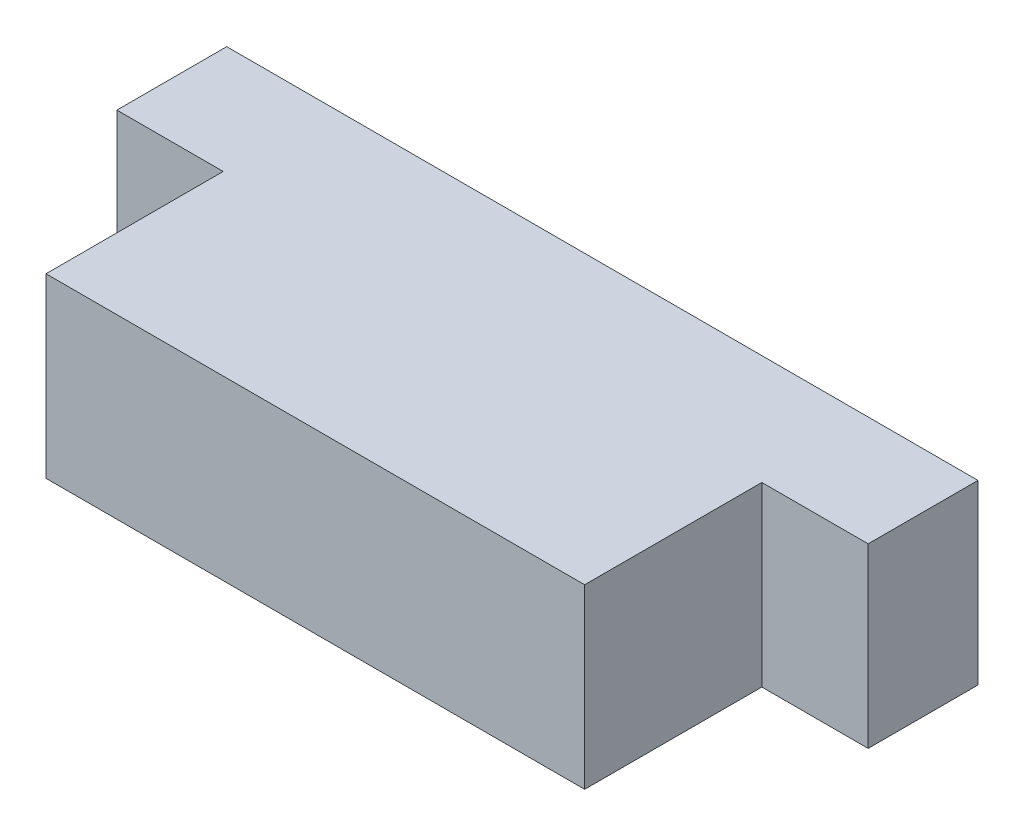
SolidWorks part; units mm, degrees
ref_plane "前视基准面" through (0, 0, 0) normal (0, 0, 1) x (1, 0, 0)
ref_plane "上视基准面" through (0, 0, 0) normal (0, 1, 0) x (1, 0, 0)
ref_plane "右视基准面" through (0, 0, 0) normal (1, 0, 0) x (0, 0, -1)
sketch "草图2" plane through (0, 0, 0) normal (0, 1, 0) x (1, 0, 0)
  line L0 (0, 0) -> (0, 5)
  line L1 (0, 5) -> (-3, 5)
  line L2 (-3, 5) -> (-3, 8.1)
  line L3 (-3, 8.1) -> (18.2, 8.1)
  line L4 (18.2, 8.1) -> (18.2, 5)
  line L5 (18.2, 5) -> (15.2, 5)
  line L6 (15.2, 5) -> (15.2, 0)
  line L7 (15.2, 0) -> (0, 0)
  dimension "D1" = 15.2
  dimension "D2" = 5
  dimension "D3" = 3
  dimension "D4" = 3.1
  dimension "D5" = 5
  dimension "D6" = 3
extrude "凸台-拉伸2" add sketch "草图2" along normal blind 5
